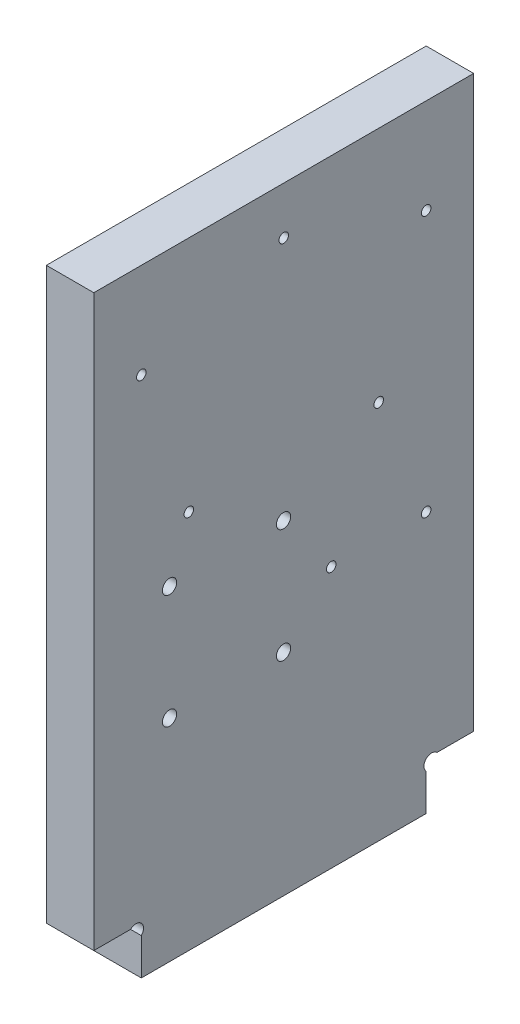
SolidWorks part; units mm, degrees
ref_plane "Plan de face" through (0, 0, 0) normal (0, 0, 1) x (1, 0, 0)
ref_plane "Plan de dessus" through (0, 0, 0) normal (0, 1, 0) x (1, 0, 0)
ref_plane "Plan de droite" through (0, 0, 0) normal (1, 0, 0) x (0, 0, -1)
sketch "Esquisse1" plane through (0, 0, 0) normal (1, 0, 0) x (0, 0, -1)
  line L8 (10, 7.7373) -> (10, 0)
  line L9 (70, 7.7373) -> (70, 0)
  line L10 (7.7373, 10) -> (0, 10)
  line L11 (10, 0) -> (70, 0)
  line L12 (72.2627, 10) -> (80, 10)
  line L13 (0, 10) -> (0, 130)
  line L14 (0, 130) -> (80, 130)
  line L15 (80, 130) -> (80, 10)
  arc A0 (10, 7.7373) -> (7.7373, 10) centre (8.8686, 8.8686) ccw
  arc A1 (70, 7.7373) -> (72.2627, 10) centre (71.1314, 8.8686) cw
  dimension "D7" = 1.1314
  dimension "D6" = 1.6
  dimension "D1" = 10
  dimension "D2" = 10
  dimension "D3" = 10
  dimension "D4" = 80
  dimension "D5" = 130
  dimension "D8" = 1.1314
  dimension "D9" = 1.1314
  dimension "D10" = 1.1314
extrude "Extrusion1" add sketch "Esquisse1" along normal blind 10
sketch "Esquisse2" plane through (10, 0, 0) normal (1, 0, 0) x (0, 0, -1)
  line L0 (0, 10) -> (7.7373, 10) construction
  line L1 (0, 130) -> (0, 10) construction
  line L2 (80, 10) -> (80, 130) construction
  line L3 (72.2627, 10) -> (80, 10) construction
  line L4 (80, 130) -> (0, 130) construction
  circle A0 centre (60, 80) radius 1
  circle A1 centre (10, 110) radius 1
  circle A2 centre (20, 80) radius 1
  circle A3 centre (70, 110) radius 1
  circle A4 centre (15.95, 68.45) radius 1.5
  circle A5 centre (15.95, 44.45) radius 1.5
  circle A6 centre (39.95, 44.45) radius 1.5
  circle A7 centre (39.95, 68.45) radius 1.5
  circle A8 centre (40, 120) radius 1
  circle A9 centre (70, 55) radius 1
  circle A10 centre (50, 55) radius 1
  dimension "D5" = 15.95
  dimension "D7" = 10
  dimension "D9" = 10
  dimension "D4" = 3
  dimension "D6" = 2
  dimension "D1" = 58.45
  dimension "D2" = 24
  dimension "D3" = 24
  dimension "D8" = 40
  dimension "D10" = 30
  dimension "D11" = 10
  dimension "D12" = 20
  dimension "D13" = 10
  dimension "D14" = 10
  dimension "D15" = 10
  dimension "D16" = 20
  dimension "D17" = 45
extrude "Enlèv. mat.-Extru.1" cut sketch "Esquisse2" against normal through all
